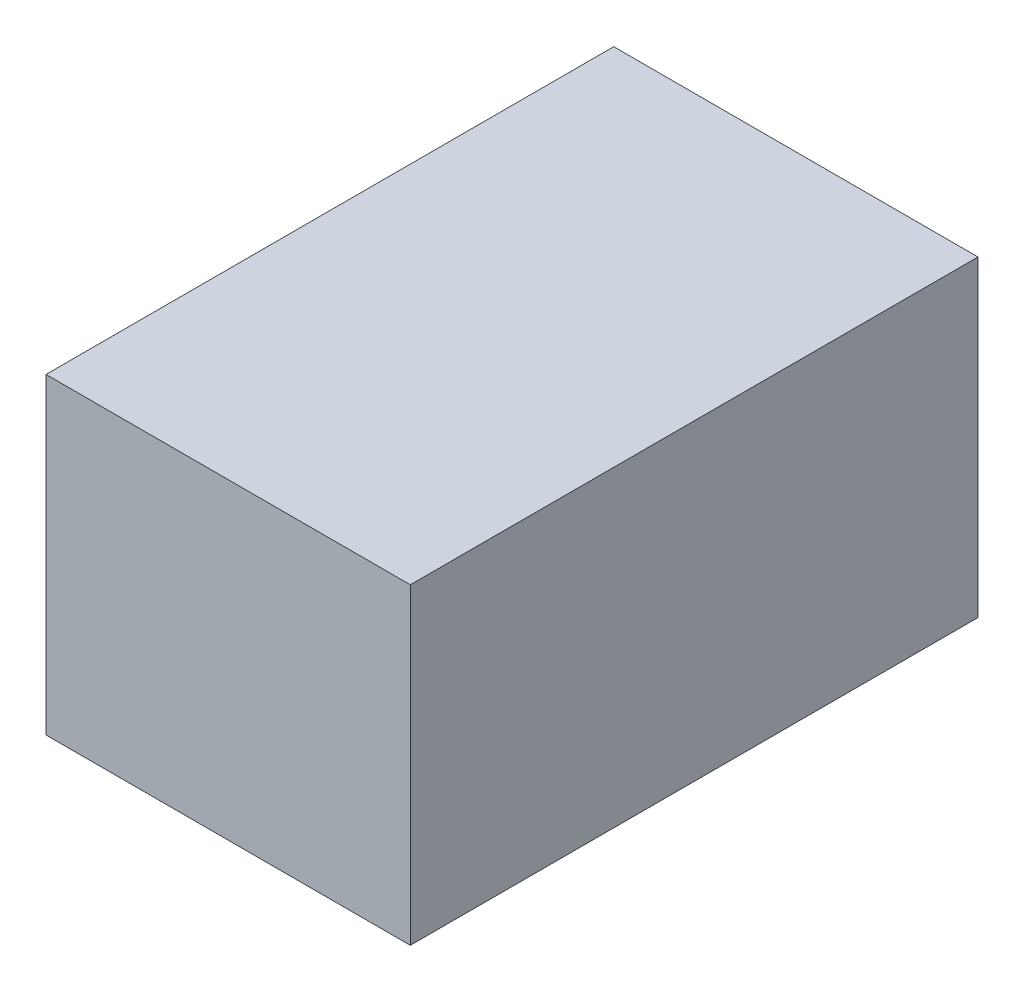
SolidWorks part; units mm, degrees
ref_plane "正面" through (0, 0, 0) normal (0, 0, 1) x (1, 0, 0)
ref_plane "平面" through (0, 0, 0) normal (0, 1, 0) x (1, 0, 0)
ref_plane "右側面" through (0, 0, 0) normal (1, 0, 0) x (0, 0, -1)
sketch "ｽｹｯﾁ1" plane through (0, 0, 0) normal (0, 0, 1) x (1, 0, 0)
  line L1 (-72.5266, -1.3894) -> (4.4734, -1.3894)
  line L2 (-72.5266, -1.3894) -> (-72.5266, 64.6106)
  line L3 (-72.5266, 64.6106) -> (4.4734, 64.6106)
  line L4 (4.4734, -1.3894) -> (4.4734, 64.6106)
  dimension "D1" = 77
  dimension "D2" = 66
extrude "ﾎﾞｽ - 押し出し1" add sketch "ｽｹｯﾁ1" along normal blind 120
